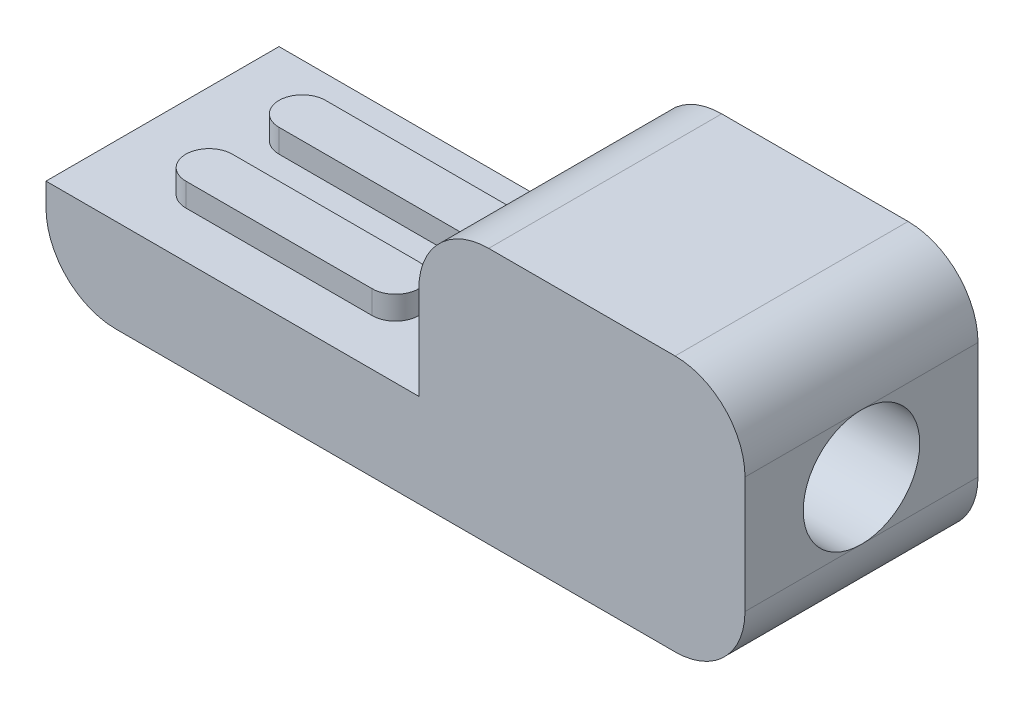
SolidWorks part; units mm, degrees
material "6061-O (SS)"
ref_plane "정면" through (0, 0, 0) normal (0, 0, 1) x (1, 0, 0)
ref_plane "윗면" through (0, 0, 0) normal (0, 1, 0) x (1, 0, 0)
ref_plane "우측면" through (0, 0, 0) normal (1, 0, 0) x (0, 0, -1)
sketch "스케치1" plane through (0, 0, 0) normal (0, 0, 1) x (1, 0, 0)
  line L0 (0, 0) -> (-15, 0)
  line L3 (-15, 0) -> (-15, 2)
  line L4 (-15, 2) -> (-7, 2)
  line L5 (-7, 2) -> (-7, 5.5)
  line L6 (-7, 5.5) -> (0, 5.5)
  line L7 (0, 5.5) -> (0, 0)
  dimension "D1" = 5.5
  dimension "D4" = 2
  dimension "D5" = 7
  dimension "D6" = 15
extrude "보스-돌출1" add sketch "스케치1" along normal mid plane 5
fillet "필렛1" radius 1.5 4 edges at (-7, 5.5, 0) (0, 0, 0) (0, 5.5, 0) (-15, 0, 0)
hole_wizard "M3 나사 구멍1" positions "스케치2" profile "스케치3" tap size "M3" standard "KS"
sketch "스케치2" plane through (0, 0, 0) normal (1, 0, 0) x (0, 0, -1)
  line L0 (-2.5, 1.5) -> (-2.5, 4) construction
  point P0 (0, 2.75)
  point P8 (-2.5, 2.75)
sketch "스케치3" plane through (0, 2.75, 0) normal (0, 1, 0) x (0, 0, -1)
  line L0 (0, 0) -> (0, 5.7511)
  line L1 (0, 5.7511) -> (1.25, 5)
  line L2 (1.25, 5) -> (1.25, 0)
  line L5 (1.25, 0) -> (0, 0)
  line L10 (0, 5.7511) -> (-1.25, 5) construction
  line L11 (0, -6.35) -> (0, 107.95) construction
  dimension "탭 드릴 지름" = 2.5
  dimension "탭 드릴 깊이" = 5
  dimension "드릴 각도" = 118
cosmetic thread "구멍 나사산1" parameters "D1"=4, "D2"=3
sketch "스케치4" plane through (0, 2, 0) normal (0, 1, 0) x (1, 0, 0)
  line L0 (-13, 1) -> (-9, 1) construction
  line L1 (-13, 1.5) -> (-9, 1.5)
  line L2 (-13, 0.5) -> (-9, 0.5)
  line L3 (-15, 0) -> (-7, 0) construction
  line L6 (-15, -2.5) -> (-15, 2.5) construction
  line L8 (-7, -2.5) -> (-7, 2.5) construction
  line L9 (-13, -1) -> (-9, -1) construction
  line L10 (-13, -1.5) -> (-9, -1.5)
  line L11 (-13, -0.5) -> (-9, -0.5)
  arc A0 (-13, 1.5) -> (-13, 0.5) centre (-13, 1) ccw
  arc A1 (-9, 0.5) -> (-9, 1.5) centre (-9, 1) ccw
  arc A2 (-13, -1.5) -> (-13, -0.5) centre (-13, -1) cw
  arc A3 (-9, -0.5) -> (-9, -1.5) centre (-9, -1) cw
  point P2 (-11, 1)
  point P18 (-11, -1)
  point P26 (-11, 0)
  dimension "D1" = 1
  dimension "D2" = 4
  dimension "D3" = 1
extrude "보스-돌출2" add sketch "스케치4" along normal blind 0.5
